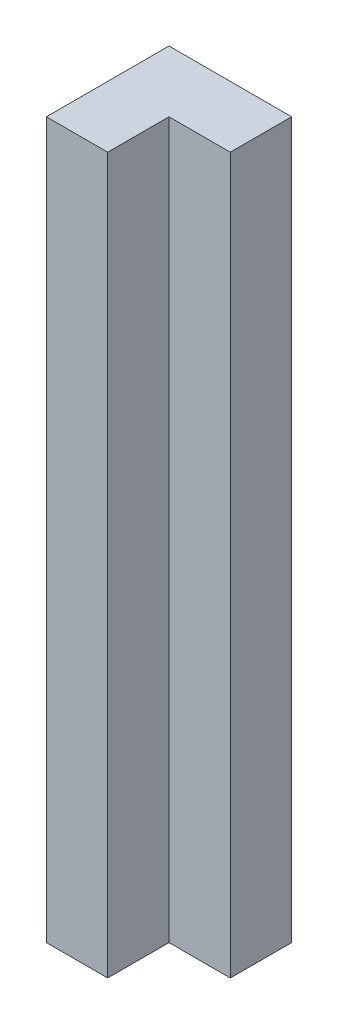
SolidWorks part; units mm, degrees
ref_plane "Ön Düzlem" through (0, 0, 0) normal (0, 0, 1) x (1, 0, 0)
ref_plane "Üst Düzlem" through (0, 0, 0) normal (0, 1, 0) x (1, 0, 0)
ref_plane "Sağ Düzlem" through (0, 0, 0) normal (1, 0, 0) x (0, 0, -1)
sketch "Sketch2" plane through (0, 0, 0) normal (0, 1, 0) x (1, 0, 0)
  line L0 (0, 0) -> (0, -6)
  line L1 (0, -6) -> (3, -6)
  line L2 (3, -6) -> (3, -3)
  line L3 (3, -3) -> (6, -3)
  line L4 (6, -3) -> (6, 0)
  line L5 (6, 0) -> (0, 0)
  dimension "D1" = 3
  dimension "D2" = 3
  dimension "D3" = 6
  dimension "D4" = 6
extrude "Boss-Extrude2" add sketch "Sketch2" along normal blind 35
